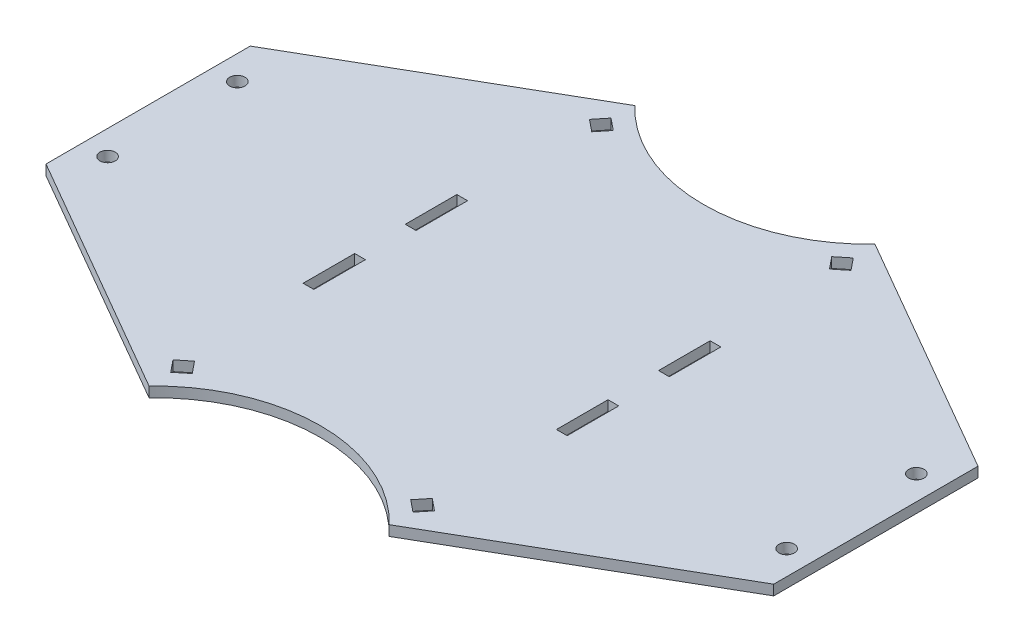
SolidWorks part; units mm, degrees
ref_plane "Plan de face" through (0, 0, 0) normal (0, 0, 1) x (1, 0, 0)
ref_plane "Plan de dessus" through (0, 0, 0) normal (0, 1, 0) x (1, 0, 0)
ref_plane "Plan de droite" through (0, 0, 0) normal (1, 0, 0) x (0, 0, -1)
sketch "Esquisse1" plane through (0, 0, 0) normal (0, 1, 0) x (1, 0, 0)
  circle A0 centre (0, 0) radius 197.5
  dimension "D1" = 395
extrude "Boss.-Extru.1" add sketch "Esquisse1" along normal blind 4
sketch "Esquisse3" plane through (0, 0, 0) normal (0, 1, 0) x (1, 0, 0)
  line L0 (-132.97, -25.4) -> (-132.97, 25.4) construction
  line L1 (-180.572, 80) -> (-157.5, 80)
  line L2 (-142.5, 65) -> (-142.5, -65)
  line L3 (-157.5, -80) -> (-180.572, -80)
  line L4 (0, -2.2) -> (0, 2.2) construction
  line L9 (-142.5, 0) -> (-197.5, 0) construction
  circle A0 centre (-132.97, 25.4) radius 3
  circle A1 centre (-132.97, -25.4) radius 3
  circle A2 centre (0, 0) radius 197.5 construction
  arc A3 (-180.572, -80) -> (-180.572, 80) centre (0, 0) cw
  arc A4 (-142.5, -65) -> (-157.5, -80) centre (-157.5, -65) cw
  arc A5 (-142.5, 65) -> (-157.5, 80) centre (-157.5, 65) ccw
  point P16 (-142.5, -80)
  point P19 (-142.5, 80)
  dimension "D1" = 6
  dimension "D8" = 15
  dimension "D2" = 25.4
  dimension "D3" = 50.8
  dimension "D4" = 160
  dimension "D6" = 9.53
  dimension "D7" = 55
extrude "Enlèv. mat.-Extru.2" cut sketch "Esquisse3" against normal through all and the other way through all
sketch "Esquisse4" plane through (0, 0, 0) normal (0, 1, 0) x (1, 0, 0)
  line L0 (-107.5, 110) -> (-107.5, 90)
  line L1 (-97.5, 120) -> (-82.5, 120)
  line L2 (-97.5, 80) -> (-82.5, 80)
  line L3 (-72.5, 110) -> (-72.5, 90)
  line L4 (-107.5, 120) -> (-72.5, 80) construction
  line L5 (-107.5, 80) -> (-72.5, 120) construction
  line L6 (-142.5, -65) -> (-142.5, 65) construction
  arc A0 (-107.5, 90) -> (-97.5, 80) centre (-97.5, 90) ccw
  arc A1 (-82.5, 80) -> (-72.5, 90) centre (-82.5, 90) ccw
  arc A2 (-72.5, 110) -> (-82.5, 120) centre (-82.5, 110) ccw
  arc A3 (-97.5, 120) -> (-107.5, 110) centre (-97.5, 110) ccw
  point P1 (-90, 100)
  dimension "D5" = 10
  dimension "D1" = 35
  dimension "D2" = 35
  dimension "D3" = 100
  dimension "D4" = 40
extrude "Enlèv. mat.-Extru.5" cut sketch "Esquisse4" along normal through all
sketch "Esquisse6" plane through (0, 0, 0) normal (0, 1, 0) x (1, 0, 0)
  line L0 (-51.7, 9.9) -> (-47.5, 9.9)
  line L1 (-51.7, 9.9) -> (-51.7, 30.1)
  line L2 (-51.7, 30.1) -> (-47.5, 30.1)
  line L3 (-47.5, 9.9) -> (-47.5, 30.1)
  line L4 (-51.7, 9.9) -> (-47.5, 30.1) construction
  line L5 (-51.7, 30.1) -> (-47.5, 9.9) construction
  line L25 (-2.75, 0) -> (2.75, 0) construction
  line L28 (-51.7, -30.1) -> (-47.5, -9.9) construction
  line L29 (-51.7, -9.9) -> (-47.5, -30.1) construction
  line L34 (-47.5, -9.9) -> (-47.5, -30.1)
  line L35 (-51.7, -30.1) -> (-47.5, -30.1)
  line L36 (-51.7, -9.9) -> (-51.7, -30.1)
  line L37 (-51.7, -9.9) -> (-47.5, -9.9)
  point P0 (-49.6, 20)
  point P24 (-49.6, -20)
  dimension "D1" = 20.2
  dimension "D2" = 4.2
  dimension "D3" = 47.5
  dimension "D4" = 20
extrude "Enlèv. mat.-Extru.8" cut sketch "Esquisse6" along normal through all
mirror "Mirror1" about plane through (0, 0, 0) normal (1, 0, 0) of "Enlèv. mat.-Extru.8", "Enlèv. mat.-Extru.5", "Enlèv. mat.-Extru.2"
sketch "Esquisse5" plane through (0, 0, 0) normal (0, 1, 0) x (1, 0, 0)
  line L0 (-65, 140) -> (65, 140) construction
  line L5 (-65, 140) -> (-65, 186.4973)
  line L6 (65, 140) -> (65, 186.4973)
  line L7 (-2.2, 0) -> (2.2, 0) construction
  line L10 (0, 140) -> (0, 0) construction
  arc A4 (180.572, 80) -> (-180.572, 80) centre (0, 0) ccw construction
  arc A9 (-65, 140) -> (65, 140) centre (0, 140) ccw
  arc A10 (-65, 186.4973) -> (65, 186.4973) centre (0, 0) cw
  dimension "D2" = 130
  dimension "D1" = 140
extrude "Enlèv. mat.-Extru.6" cut sketch "Esquisse5" along normal through all
mirror "Mirror2" about plane through (0, 0, 0) normal (0, 0, 1) of "Enlèv. mat.-Extru.6"
sketch "Sketch1" plane through (0, 4, 0) normal (0, 1, 0) x (1, 0, 0)
  line L0 (0, -75) -> (-65, -75) construction
  line L1 (-65, -75) -> (-65, -140) construction
  line L2 (-47.442, -86.2195) -> (-51.2195, -81.558)
  line L3 (-47.442, -86.2195) -> (-42.7805, -82.442)
  line L4 (-51.2195, -81.558) -> (-46.558, -77.7805)
  line L5 (-42.7805, -82.442) -> (-46.558, -77.7805)
  line L6 (-45.1112, -84.3308) -> (-40.9229, -89.4994) construction
  line L7 (-65, -109.0101) -> (-23.0301, -75) construction
  line L8 (-46.558, -77.7805) -> (-47.442, -86.2195) construction
  arc A0 (65, -140) -> (-65, -140) centre (0, -140) ccw construction
  circle A1 centre (-47, -82) radius 3 construction
  circle A2 centre (-47, -82) radius 7 construction
  circle A3 centre (-47, -82) radius 5.5 construction
  point P16 (-47, -82)
  point P22 (-48.8888, -79.6692)
  dimension "D1" = 6
  dimension "D2" = 14
  dimension "D3" = 11
  dimension "D4" = 47
extrude "Cut-Extrude1" cut sketch "Sketch1" against normal through all
mirror "Mirror4" about plane through (0, 0, 0) normal (0, 0, 1) of "Cut-Extrude1"
mirror "Mirror5" about plane through (0, 0, 0) normal (1, 0, 0) of "Mirror4", "Cut-Extrude1"
sketch "Sketch3" plane through (0, 4, 0) normal (0, 1, 0) x (1, 0, 0)
  line L0 (-47.0227, 95.1239) -> (-142.5, 40)
  line L1 (-142.5, -65) -> (-142.5, 65) construction
  line L2 (-47.0227, 95.1239) -> (-47.0227, 40) construction
  line L3 (-47.0227, 40) -> (-142.5, 40) construction
  line L4 (-142.5, 40) -> (-180.572, 80)
  line L5 (-180.572, 80) -> (-180.572, 186.4973)
  line L6 (-180.572, 186.4973) -> (-65, 186.4973)
  line L7 (-65, 186.4973) -> (-47.0227, 95.1239)
  line L8 (-180.572, -80) -> (-157.5, -80) construction
  arc A0 (-65, 140) -> (65, 140) centre (0, 140) ccw construction
  dimension "D1" = 30
  dimension "D2" = 120
extrude "Cut-Extrude2" cut sketch "Sketch3" against normal through all
mirror "Mirror6" about plane through (0, 0, 0) normal (0, 0, 1) of "Cut-Extrude2"
mirror "Mirror7" about plane through (0, 0, 0) normal (1, 0, 0) of "Mirror6", "Cut-Extrude2"
